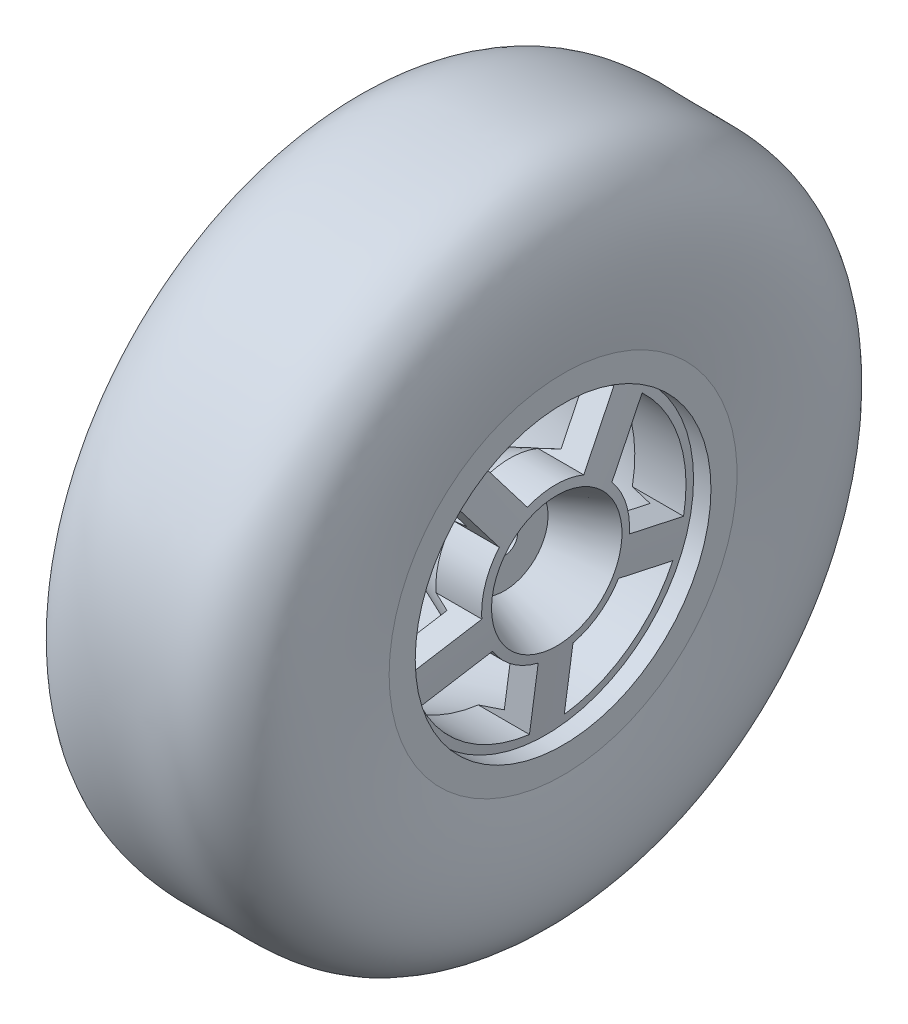
SolidWorks part; units mm, degrees
ref_plane "Front Plane" through (0, 0, 0) normal (0, 0, 1) x (1, 0, 0)
ref_plane "Top Plane" through (0, 0, 0) normal (0, 1, 0) x (1, 0, 0)
ref_plane "Right Plane" through (0, 0, 0) normal (1, 0, 0) x (0, 0, -1)
sketch "Sketch2" plane through (0, 0, 0) normal (0, 0, 1) x (1, 0, 0)
  line L0 (0, 31.7811) -> (0, -27.8084) construction
  line L1 (-63.1838, 0) -> (56.9411, 0) construction
  line L3 (0, 4.5) -> (11.7212, 9.3839)
  line L4 (11.7212, 9.3839) -> (10.9699, 15)
  line L5 (10.9699, 15) -> (-10, 22)
  line L6 (-10, 22) -> (-10, 23)
  line L7 (-10, 23) -> (-9.5, 23)
  line L8 (0, 0) -> (9, 0)
  line L9 (0, 4.5) -> (-1.5, 4.5)
  line L10 (9, 0) -> (9, 5)
  line L11 (9, 5) -> (15, 7.5)
  line L12 (15, 7.5) -> (13.7291, 17)
  line L13 (13.7291, 17) -> (15.7291, 17)
  line L14 (15.7291, 17) -> (15.7291, 20)
  line L15 (-1.5, 4.5) -> (-1.5, 0)
  line L16 (-1.5, 0) -> (9, 0)
  line L17 (-1.5, 0) -> (0, 0)
  spline S0 degree 3 poles (-9.5, 23) (-9.1846, 24.8052) (-11.6806, 29.4814) (-6.2282, 39.1909) (6.2493, 37.878) (13.0434, 39.5085) (17.6038, 30.6245) (15.7291, 20) knots 0 0 0 0 0.229958 0.280779 0.508213 0.824609 1 1 1 1
  point P13 (-8.9021, 34.3459)
  point P20 (3.2854, 38.5)
  point P21 (0, 0)
  point P22 (0, 0)
  dimension "D2" = 10
  dimension "D3" = 3
  dimension "D4" = 3
  dimension "D5" = 15
  dimension "D6" = 6
  dimension "D7" = 105
  dimension "D8" = 34
  dimension "D9" = 2
  dimension "D10" = 3
  dimension "D11" = 44
  dimension "D12" = 30
  dimension "D13" = 25
  dimension "D14" = 0.5
  dimension "D15" = 1
  dimension "D16" = 77
  dimension "D17" = 8.5
  dimension "D18" = 9
revolve "Revolve1" add sketch "Sketch2" angle 360 about L1
sketch "Sketch3" plane through (9, 0, 0) normal (1, 0, 0) x (0, 0, -1)
  circle A0 centre (0, 0) radius 1.5
  dimension "D1" = 3
extrude "Cut-Extrude1" cut sketch "Sketch3" against normal up to next
sketch "Sketch4" plane through (15.7291, 0, 0) normal (1, 0, 0) x (0, 0, -1)
  line L0 (-9.4046, 12.9443) -> (0, 0) construction
  line L1 (0, -16) -> (15.2169, -4.9443)
  line L2 (15.2169, -4.9443) -> (9.4046, 12.9443)
  line L3 (9.4046, 12.9443) -> (-9.4046, 12.9443)
  line L4 (-9.4046, 12.9443) -> (-15.2169, -4.9443)
  line L5 (-15.2169, -4.9443) -> (0, -16)
  line L6 (0, 0) -> (9.4046, 12.9443) construction
  line L7 (-15.2169, -4.9443) -> (0, 0) construction
  line L8 (0, -16) -> (0, 0) construction
  line L9 (15.2169, -4.9443) -> (0, 0) construction
  line L10 (-11.0226, 11.7687) -> (-1.618, -1.1756)
  line L11 (1.618, -1.1756) -> (11.0226, 11.7687)
  line L12 (15.8349, -3.0422) -> (0.618, 1.9021)
  line L13 (2, -16) -> (2, 0)
  line L14 (-14.5989, -6.8464) -> (0.618, -1.9021)
  line L15 (-7.7865, 14.1198) -> (1.618, 1.1756)
  line L16 (-1.618, 1.1756) -> (7.7865, 14.1198)
  line L17 (14.5989, -6.8464) -> (-0.618, -1.9021)
  line L18 (-2, -16) -> (-2, 0)
  line L19 (-15.8349, -3.0422) -> (-0.618, 1.9021)
  circle A2 centre (0, 0) radius 16
  circle A3 centre (0, 0) radius 16
  circle A4 centre (0, 0) radius 12.9443 construction
  circle A5 centre (0, 0) radius 8.5
  circle A6 centre (0, 0) radius 8.5
  dimension "D1" = 1
  dimension "D2" = 1
  dimension "D3" = 2
  dimension "D4" = 2
extrude "Cut-Extrude2" cut sketch "Sketch4" against normal through all contours L16 A3 L15 L3 | A6 L16 L3 L15 | L12 A3 L11 L2 | A6 L12 L2 L11 | L13 A3 L17 L1 | A6 L13 L1 L17 | L14 A3 L18 L5 | A6 L14 L5 L18 | L10 A3 L19 L4 | A6 L10 L4 L19
sketch "Sketch5" plane through (-1.5, 0, 0) normal (-1, 0, 0) x (0, 0, 1)
  line L1 (0, -2.8868) -> (2.5, -1.4434)
  line L2 (2.5, -1.4434) -> (2.5, 1.4434)
  line L3 (2.5, 1.4434) -> (0, 2.8868)
  line L4 (0, 2.8868) -> (-2.5, 1.4434)
  line L5 (-2.5, 1.4434) -> (-2.5, -1.4434)
  line L6 (-2.5, -1.4434) -> (0, -2.8868)
  circle A0 centre (0, 0) radius 2.5 construction
  dimension "D1" = 5
extrude "Cut-Extrude3" cut sketch "Sketch5" against normal blind 10
